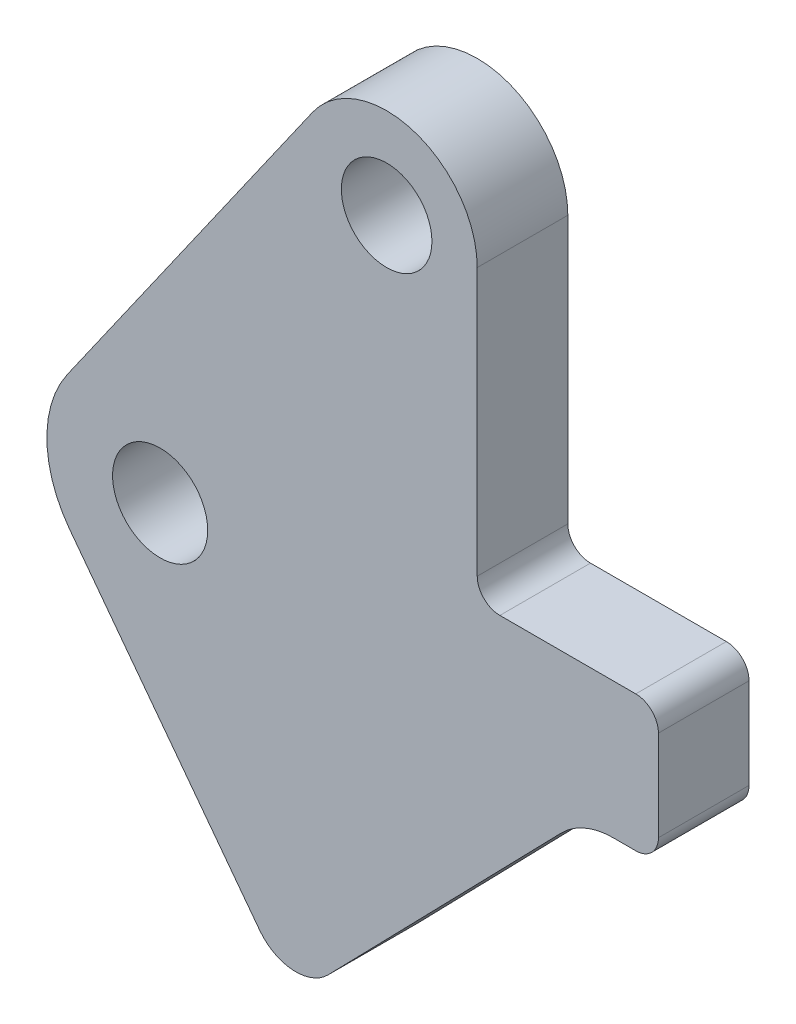
SolidWorks part; units mm, degrees
material "Thornel Mat VMA"
ref_plane "前视基准面" through (0, 0, 0) normal (0, 0, 1) x (1, 0, 0)
ref_plane "上视基准面" through (0, 0, 0) normal (0, 1, 0) x (1, 0, 0)
ref_plane "右视基准面" through (0, 0, 0) normal (1, 0, 0) x (0, 0, -1)
sketch "草图1" plane through (0, 0, 0) normal (0, 0, 1) x (1, 0, 0)
  line L0 (0, 0) -> (10, 0) construction
  line L1 (10, -1.4) -> (10.5, -1.4)
  line L2 (11, -0.9) -> (11, 1.1)
  line L3 (3.3626, 9.1484) -> (-2.0468, 1.4355)
  line L4 (-1.9966, -1.5045) -> (2.1964, -7.0688)
  line L5 (3.7115, -7.1647) -> (8.8537, -1.8838)
  line L6 (10, 0) -> (10, -3) construction
  line L7 (7, 8) -> (7, 2.1)
  line L8 (7.5, 1.6) -> (10.5, 1.6)
  line L9 (5, 8) -> (5, 0) construction
  circle A0 centre (0, 0) radius 1.05
  arc A1 (10, -1.4) -> (8.8537, -1.8838) centre (10, -3) ccw
  arc A2 (-2.0468, 1.4355) -> (-1.9966, -1.5045) centre (0, 0) ccw
  arc A3 (2.1964, -7.0688) -> (3.7115, -7.1647) centre (2.995, -6.467) ccw
  arc A5 (3.3626, 9.1484) -> (7, 8) centre (5, 8) cw
  circle A6 centre (5, 8) radius 1
  arc A7 (10.5, -1.4) -> (11, -0.9) centre (10.5, -0.9) ccw
  arc A8 (7, 2.1) -> (7.5, 1.6) centre (7.5, 2.1) ccw
  arc A9 (11, 1.1) -> (10.5, 1.6) centre (10.5, 1.1) ccw
  point P15 (2.8981, -8)
  point P24 (11, -1.4)
  point P29 (11, 1.6)
  dimension "D1" = 2.1
  dimension "D3" = 3.2
  dimension "D4" = 2.5
  dimension "D7" = 1
  dimension "D10" = 2
  dimension "D12" = 2
  dimension "D15" = 0.5
  dimension "D2" = 10
  dimension "D5" = 3
  dimension "D6" = 8
  dimension "D8" = 3
  dimension "D9" = 1
  dimension "D11" = 53
  dimension "D13" = 8
  dimension "D14" = 5
extrude "凸台-拉伸1" add sketch "草图1" along normal blind 2
